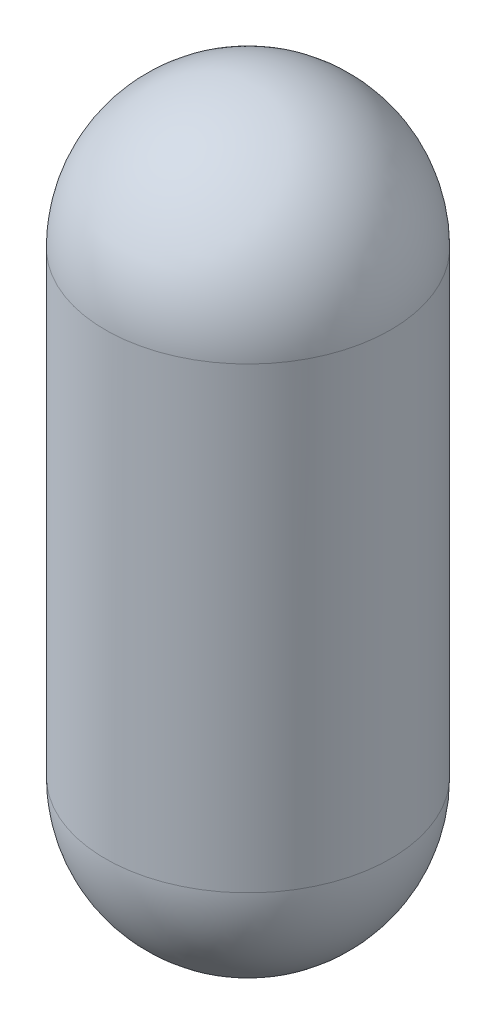
SolidWorks part; units mm, degrees
material "Titanium"
ref_plane "Front Plane" through (0, 0, 0) normal (0, 0, 1) x (1, 0, 0)
ref_plane "Top Plane" through (0, 0, 0) normal (0, 1, 0) x (1, 0, 0)
ref_plane "Right Plane" through (0, 0, 0) normal (1, 0, 0) x (0, 0, -1)
sketch "Sketch1" plane through (0, 0, 0) normal (0, 0, 1) x (1, 0, 0)
  line L0 (0, 1815.66) -> (0, 1818.2)
  line L2 (0, 0) -> (0, 1386.4) construction
  line L4 (431.8, 0) -> (431.8, 1386.4)
  line L5 (0, -431.8) -> (0, -429.26)
  line L6 (0, 976.2421) -> (431.8, 976.2421) construction
  line L7 (429.26, 1386.4) -> (429.26, 0)
  line L8 (429.26, 319.1286) -> (431.8, 319.1286) construction
  line L9 (0, 1386.4) -> (0, 1815.66) construction
  line L10 (0, 0) -> (0, -429.26) construction
  arc A2 (431.8, 1386.4) -> (0, 1818.2) centre (0, 1386.4) ccw
  arc A3 (0, -431.8) -> (431.8, 0) centre (0, 0) ccw
  arc A4 (429.26, 1386.4) -> (0, 1815.66) centre (0, 1386.4) ccw
  arc A5 (429.26, 0) -> (0, -429.26) centre (0, 0) cw
  dimension "D3" = 2.54
  dimension "D4" = 429.26
  dimension "D5" = 431.8
  dimension "D6" = 431.8
  dimension "D1" = 2250
  dimension "D2" = 431.8
revolve "Revolve1" add sketch "Sketch1" angle 360 about L2
